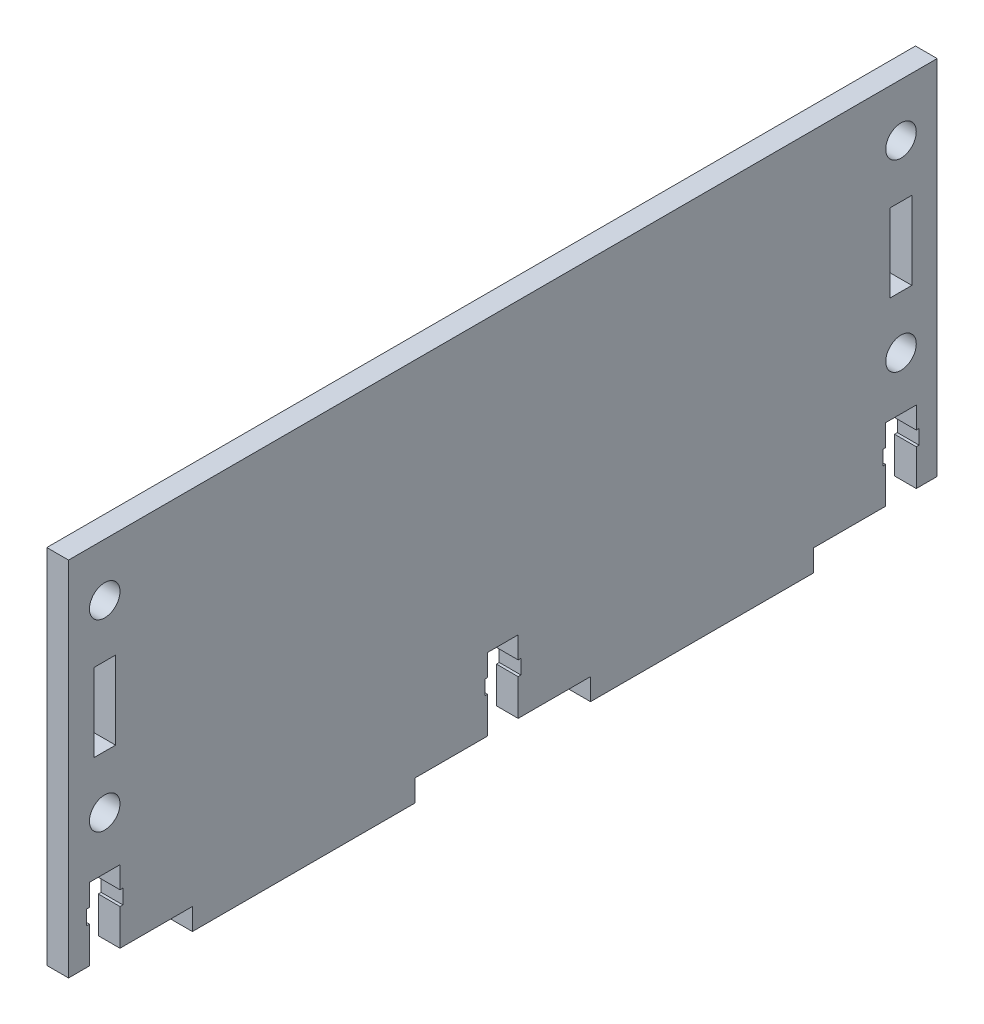
SolidWorks part; units mm, degrees
ref_plane "Front Plane" through (0, 0, 0) normal (0, 0, 1) x (1, 0, 0)
ref_plane "Top Plane" through (0, 0, 0) normal (0, 1, 0) x (1, 0, 0)
ref_plane "Right Plane" through (0, 0, 0) normal (1, 0, 0) x (0, 0, -1)
sketch "Sketch2" plane through (0, 0, 0) normal (1, 0, 0) x (0, 0, -1)
  line L0 (0, 0) -> (2.89, 0)
  line L1 (0, 0) -> (0, 50)
  line L2 (0, 50) -> (120, 50)
  line L3 (120, 50) -> (120, 0)
  line L4 (112.5, 5) -> (112.5, 7)
  line L5 (47.89, -3) -> (47.89, 0)
  line L7 (7.11, 0) -> (7.11, 5)
  line L8 (7.11, 5) -> (7.5, 5)
  line L9 (7.5, 5) -> (7.5, 7)
  line L10 (7.5, 7) -> (7.11, 7)
  line L11 (7.11, 7) -> (7.11, 10)
  line L13 (7.11, 10) -> (2.89, 10)
  line L14 (2.89, 10) -> (2.89, 7)
  line L15 (2.89, 7) -> (2.5, 7)
  line L16 (2.5, 7) -> (2.5, 5)
  line L17 (2.5, 5) -> (2.89, 5)
  line L18 (2.89, 5) -> (2.89, 0)
  line L19 (117.11, 5) -> (117.11, 0)
  line L20 (117.5, 5) -> (117.11, 5)
  line L21 (117.5, 7) -> (117.5, 5)
  line L22 (117.11, 7) -> (117.5, 7)
  line L23 (117.11, 10) -> (117.11, 7)
  line L24 (112.89, 10) -> (117.11, 10)
  line L25 (112.89, 7) -> (112.89, 10)
  line L26 (112.5, 7) -> (112.89, 7)
  line L27 (112.89, 5) -> (112.5, 5)
  line L28 (112.89, 0) -> (112.89, 5)
  line L30 (47.89, 0) -> (57.89, 0)
  line L31 (17.11, -3) -> (17.11, 0)
  line L32 (17.11, -3) -> (47.89, -3)
  line L33 (62.11, 10) -> (57.89, 10)
  line L34 (7.11, 0) -> (17.11, 0)
  line L35 (62.11, 0) -> (62.11, 5)
  line L36 (62.11, 5) -> (62.5, 5)
  line L37 (62.5, 7) -> (62.11, 7)
  line L38 (62.11, 7) -> (62.11, 10)
  line L39 (57.89, 10) -> (57.89, 7)
  line L40 (57.89, 7) -> (57.5, 7)
  line L41 (57.5, 7) -> (57.5, 5)
  line L42 (57.5, 5) -> (57.89, 5)
  line L43 (57.89, 5) -> (57.89, 0)
  line L44 (62.5, 5) -> (62.5, 7)
  line L45 (102.89, -3) -> (102.89, 0)
  line L46 (72.11, -3) -> (72.11, 0)
  line L47 (102.89, -3) -> (72.11, -3)
  line L48 (102.89, 0) -> (112.89, 0)
  line L49 (62.11, 0) -> (72.11, 0)
  line L50 (117.11, 0) -> (120, 0)
  line L51 (116.5, 24.61) -> (113.5, 24.61)
  line L52 (3.5, 35.39) -> (6.5, 35.39)
  line L53 (3.5, 35.39) -> (3.5, 24.61)
  line L54 (113.5, 35.39) -> (113.5, 24.61)
  line L55 (3.5, 24.61) -> (6.5, 24.61)
  line L56 (6.5, 35.39) -> (6.5, 24.61)
  line L57 (116.5, 35.39) -> (113.5, 35.39)
  line L58 (116.5, 35.39) -> (116.5, 24.61)
extrude "Boss-Extrude2" add sketch "Sketch2" along normal blind 3
sketch "Sketch7" plane through (3, 0, 0) normal (1, 0, 0) x (0, 0, -1)
  line L0 (5, 24.61) -> (5, 10)
  line L1 (6.5, 35.39) -> (3.5, 35.39) construction
  line L2 (5, 35.39) -> (5, 50)
  line L3 (120, 50) -> (0, 50) construction
  line L4 (3.5, 24.61) -> (6.5, 24.61) construction
  line L5 (2.89, 10) -> (7.11, 10) construction
  line L8 (115, 35.39) -> (115, 50)
  line L9 (115, 24.61) -> (115, 10)
hole_wizard "Hole for M3 300® SC Nuts (SP)1" positions "Sketch8" profile "Sketch9" hole size "M3x0.5" standard "PEM® Metric" end condition through all
sketch "Sketch8" plane through (3, 0, 0) normal (1, 0, 0) x (0, 0, -1)
  line L0 (5, 35.39) -> (5, 50) construction
  line L1 (5, 24.61) -> (5, 10) construction
  line L2 (115, 35.39) -> (115, 50) construction
  line L3 (115, 24.61) -> (115, 10) construction
  point P0 (5, 42.695)
  point P4 (5, 17.305)
  point P8 (115, 42.695)
  point P12 (115, 17.305)
sketch "Sketch9" plane through (3, 42.695, -5) normal (0, 1, 0) x (0, 0, -1)
  line L0 (0, 0) -> (0, 3)
  line L1 (0, 3) -> (2.11, 3)
  line L2 (2.11, 3) -> (2.11, 0)
  line L5 (2.11, 0) -> (0, 0)
  line L11 (0, -6.35) -> (0, 107.95) construction
  dimension "Thru Hole Dia." = 4.22
  dimension "Thru Hole Depth" = 3
